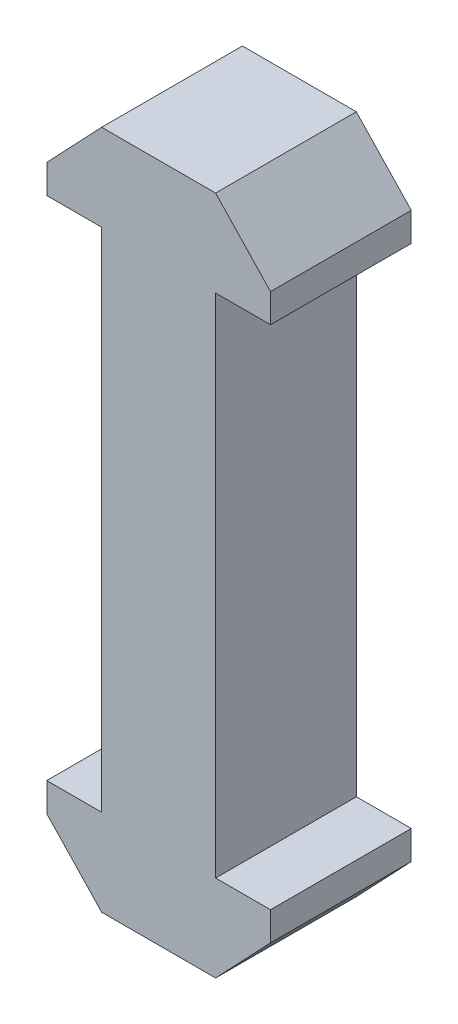
SolidWorks part; units mm, degrees
ref_plane "Front Plane" through (0, 0, 0) normal (0, 0, 1) x (1, 0, 0)
ref_plane "Top Plane" through (0, 0, 0) normal (0, 1, 0) x (1, 0, 0)
ref_plane "Right Plane" through (0, 0, 0) normal (1, 0, 0) x (0, 0, -1)
sketch "Sketch1" plane through (0, 0, 0) normal (0, 0, 1) x (1, 0, 0)
  line L3 (0, 0) -> (0, 18) construction
  line L8 (0, 18) -> (-8.6643, 18) construction
  line L14 (-4.05, 0) -> (-4.05, 36)
  line L15 (4.05, 0) -> (4.05, 36)
  point P5 (-4.05, 18)
  point P6 (4.05, 18)
  line B0 (7.95, 0) -> (7.95, -2.04)
  line B1 (4.048, -6.1524) -> (-4.048, -6.1524)
  line B2 (-7.95, -2.04) -> (-7.95, 0)
  line B3 (-7.95, 0) -> (7.95, 0)
  line B4 (7.95, -2.04) -> (4.048, -6.1524)
  line B5 (-4.048, -6.1524) -> (-7.95, -2.04)
  line B6 (4.05, 0) -> (-4.05, 0) construction
  line B7 (7.95, 36) -> (7.95, 38.04)
  line B8 (4.048, 42.1524) -> (-4.048, 42.1524)
  line B9 (-7.95, 38.04) -> (-7.95, 36)
  line B10 (-7.95, 36) -> (7.95, 36)
  line B11 (7.95, 38.04) -> (4.048, 42.1524)
  line B12 (-4.048, 42.1524) -> (-7.95, 38.04)
  line B13 (4.05, 36) -> (-4.05, 36) construction
  dimension "D1" = 36
sketch_block_instance "Block1-1"
sketch_block "Block1" parameters "D1"=8.44, "D2"=2.6, "D3"=6, "D4"=16.7, "D6"=5.6686, "D7"=2.0404, "D8"=8.0963, "D9"=15.9, "D5"=2.4157
sketch_block_instance "Block1-5"
extrude "Boss-Extrude1" add sketch "Sketch1" along normal mid plane 10
